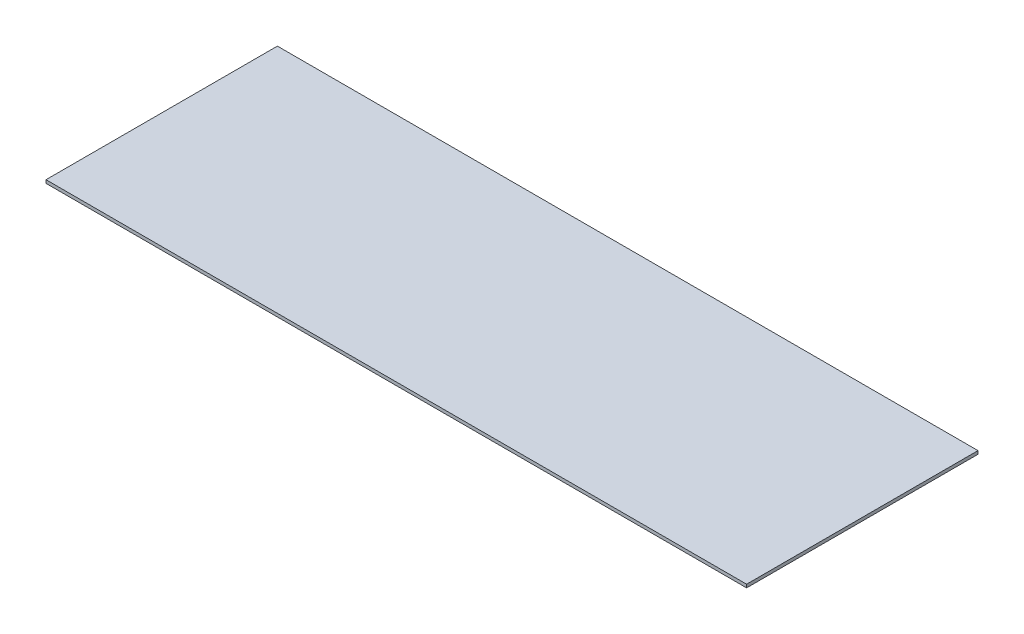
SolidWorks part; units mm, degrees
ref_plane "Front" through (0, 0, 0) normal (0, 0, 1) x (1, 0, 0)
ref_plane "Top" through (0, 0, 0) normal (0, 1, 0) x (1, 0, 0)
ref_plane "Right" through (0, 0, 0) normal (1, 0, 0) x (0, 0, -1)
sketch "Sketch1" plane through (0, 0, 0) normal (0, 1, 0) x (1, 0, 0)
  line L1 (-1047.6487, 331.7391) -> (42.3513, 331.7391)
  line L2 (-1047.6487, 331.7391) -> (-1047.6487, -28.2609)
  line L3 (-1047.6487, -28.2609) -> (42.3513, -28.2609)
  line L4 (42.3513, 331.7391) -> (42.3513, -28.2609)
  dimension "D1" = 1090
  dimension "D2" = 360
extrude "Boss-Extrude1" add sketch "Sketch1" along normal blind 5
